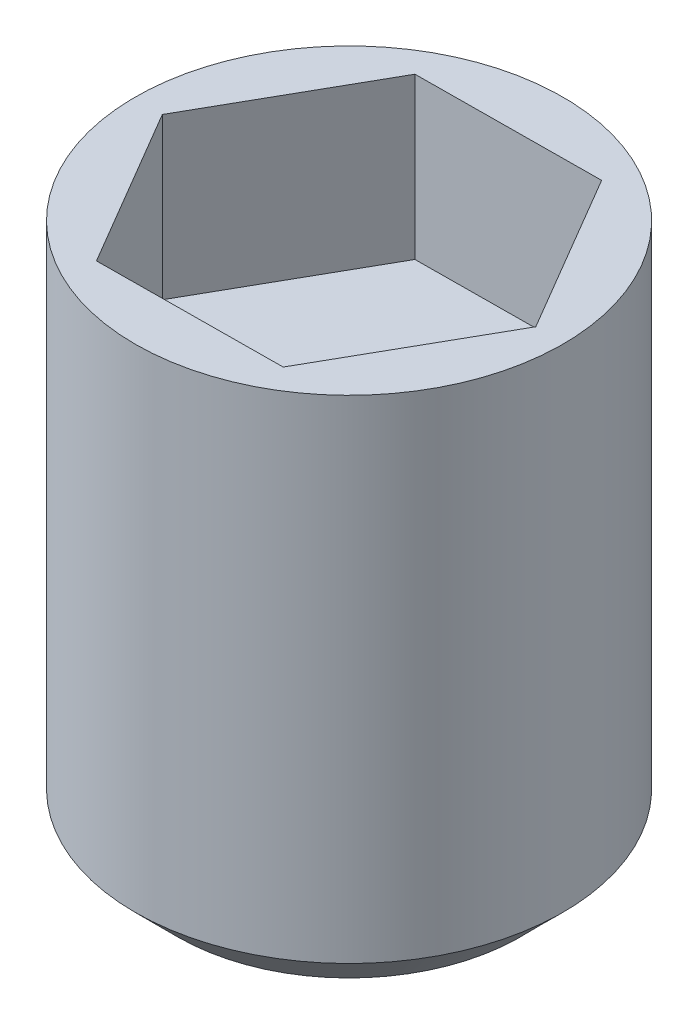
SolidWorks part; units mm, degrees
ref_plane "Спереди" through (0, 0, 0) normal (0, 0, 1) x (1, 0, 0)
ref_plane "Сверху" through (0, 0, 0) normal (0, 1, 0) x (1, 0, 0)
ref_plane "Справа" through (0, 0, 0) normal (1, 0, 0) x (0, 0, -1)
sketch "Эскиз1" plane through (0, 0, 0) normal (0, 0, 1) x (1, 0, 0)
  line L0 (0, 0) -> (3.2, 0)
  line L2 (4, 10) -> (4, 0.8)
  line L3 (4, 0.8) -> (3.2, 0)
  line L4 (4, 10) -> (0, 10)
  line L5 (0, 68.6446) -> (0, -29.1082) construction
  line L6 (0, 0) -> (0, 10)
  point P1 (0, 0)
  point P4 (0, 0)
  point P9 (3.7931, 0)
  point P10 (0, 0)
  point P11 (0, 0)
  point P13 (0, 0)
revolve "Повернуть1" add sketch "Эскиз1" angle 360 about L5
sketch "Эскиз2" plane through (0, 10, 0) normal (0, 1, 0) x (1, 0, 0)
  line L1 (1.7553, -2.9865) -> (3.464, 0.0269)
  line L2 (3.464, 0.0269) -> (1.7087, 3.0133)
  line L3 (1.7087, 3.0133) -> (-1.7553, 2.9865)
  line L4 (-1.7553, 2.9865) -> (-3.464, -0.0269)
  line L5 (-3.464, -0.0269) -> (-1.7087, -3.0133)
  line L6 (-1.7087, -3.0133) -> (1.7553, -2.9865)
  circle A0 centre (0, 0) radius 3 construction
extrude "Вырез-Вытянуть1" cut sketch "Эскиз2" against normal blind 3
